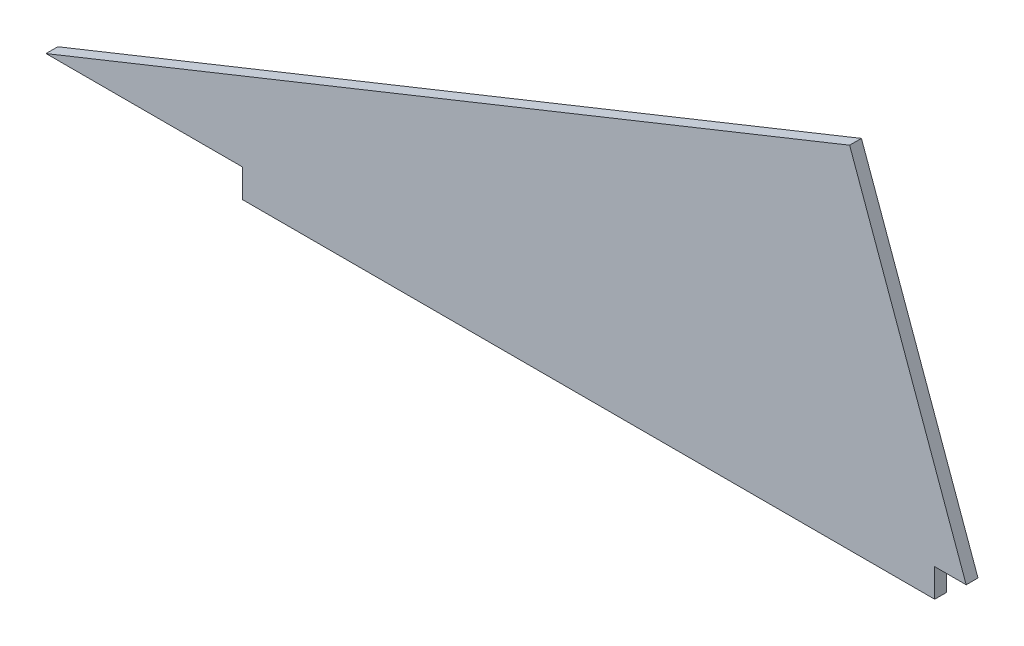
SolidWorks part; units mm, degrees
ref_plane "Front Plane" through (0, 0, 0) normal (0, 0, 1) x (1, 0, 0)
ref_plane "Top Plane" through (0, 0, 0) normal (0, 1, 0) x (1, 0, 0)
ref_plane "Right Plane" through (0, 0, 0) normal (1, 0, 0) x (0, 0, -1)
sketch "Sketch2" plane through (0, 0, 0) normal (0, 0, 1) x (1, 0, 0)
  line L2 (371, -20.34) -> (324, 109.66)
  line L3 (324, 109.66) -> (0, -20.34)
  line L5 (371, -20.34) -> (358.3, -20.34)
  line L6 (358.3, -20.34) -> (358.3, -31.74)
  line L7 (358.3, -31.74) -> (79.3, -31.74)
  line L8 (79.3, -31.74) -> (79.3, -20.34)
  line L9 (79.3, -20.34) -> (0, -20.34)
  dimension "D1" = 371
  dimension "D2" = 12.7
  dimension "D3" = 279
  dimension "D4" = 130
  dimension "D5" = 324
  dimension "D6" = 11.4
  dimension "D7" = 11.4
extrude "Boss-Extrude1" add sketch "Sketch2" along normal blind 4.76
